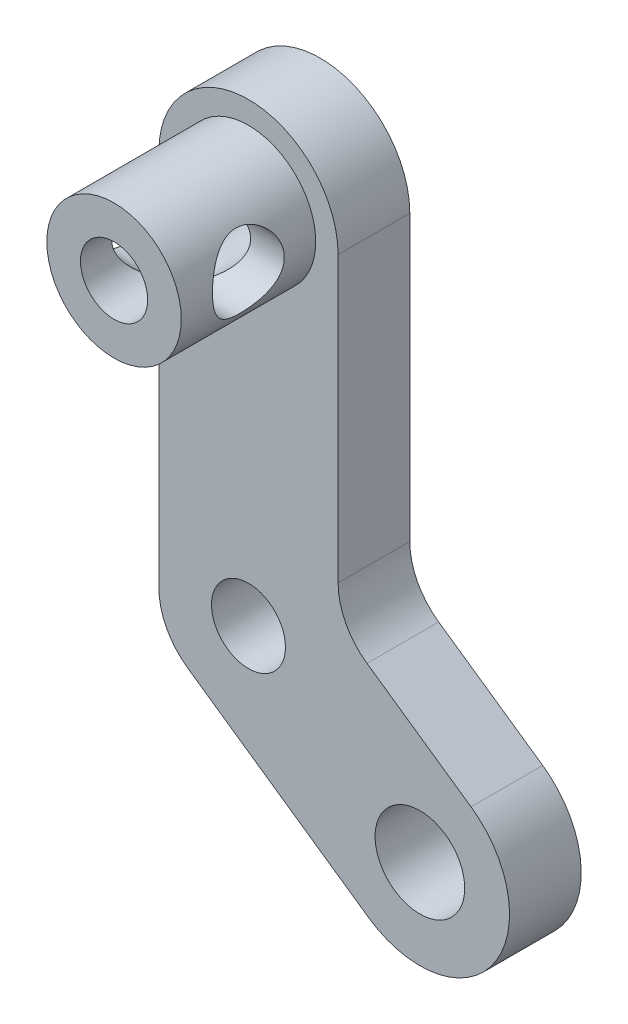
SolidWorks part; units mm, degrees
ref_plane "Front Plane" through (0, 0, 0) normal (0, 0, 1) x (1, 0, 0)
ref_plane "Top Plane" through (0, 0, 0) normal (0, 1, 0) x (1, 0, 0)
ref_plane "Right Plane" through (0, 0, 0) normal (1, 0, 0) x (0, 0, -1)
sketch "Sketch1" plane through (0, 0, 0) normal (0, 0, 1) x (1, 0, 0)
  line L0 (0, 0) -> (7.65, -5.313) construction
  line L1 (0, 0) -> (0, 16.35) construction
  line L2 (-4, -0.523) -> (-4, 16.35)
  line L3 (-2.7113, -2.987) -> (5.3683, -8.5984)
  line L4 (4, 3.661) -> (4, 16.35)
  line L5 (5.2887, 1.197) -> (9.9317, -2.0276)
  line L6 (4, 2.092) -> (4, 16.35) construction
  line L7 (4, 2.092) -> (9.9317, -2.0276) construction
  line L8 (-4, -2.092) -> (-4, 16.35) construction
  line L9 (-4, -2.092) -> (5.3683, -8.5984) construction
  circle A0 centre (7.65, -5.313) radius 2
  circle A1 centre (0, 0) radius 1.65
  arc A2 (-4, 16.35) -> (4, 16.35) centre (0, 16.35) cw
  arc A3 (5.3683, -8.5984) -> (9.9317, -2.0276) centre (7.65, -5.313) ccw
  arc A4 (4, 3.661) -> (5.2887, 1.197) centre (7, 3.661) ccw
  arc A5 (-4, -0.523) -> (-2.7113, -2.987) centre (-1, -0.523) ccw
  dimension "D1" = 4
  dimension "D3" = 3
  dimension "D2" = 4
extrude "Boss-Extrude1" add sketch "Sketch1" along normal blind 3.2
sketch "Sketch5" plane through (0, 0, 3.2) normal (0, 0, 1) x (1, 0, 0)
  circle A0 centre (0, 16.35) radius 3
extrude "Boss-Extrude2" add sketch "Sketch5" along normal blind 6
hole_wizard "CSK for M3 Flat Head Machine Screw2" positions "Sketch7" profile "Sketch6" countersink size "M3" standard "Ansi Metric" end condition through all
sketch "Sketch7" plane through (0, 0, 0) normal (0, 0, -1) x (-1, 0, 0)
  point P0 (0, 16.35)
sketch "Sketch6" plane through (0, 16.35, 0) normal (1, 0, 0) x (0, 1, 0)
  line L0 (0, 0) -> (0, 9.2)
  line L1 (0, 9.2) -> (1.5, 9.2)
  line L2 (1.5, 9.2) -> (1.5, 1.5)
  line L3 (1.5, 1.5) -> (3, 0)
  line L5 (3, 0) -> (0, 0)
  line L6 (-1.5, 1.5) -> (-3, 0) construction
  line L11 (0, -6.35) -> (0, 107.95) construction
  dimension "Thru Hole Dia." = 3
  dimension "Thru Hole Depth" = 9.2
  dimension "Near C'Sink Dia." = 6
  dimension "Near C'Sink Angle" = 90
sketch "Sketch8" plane through (4, 0, 0) normal (1, 0, 0) x (0, 0, -1)
  circle A0 centre (-6.2, 16.5) radius 1.6
extrude "Cut-Extrude2" cut sketch "Sketch8" against normal blind 16
